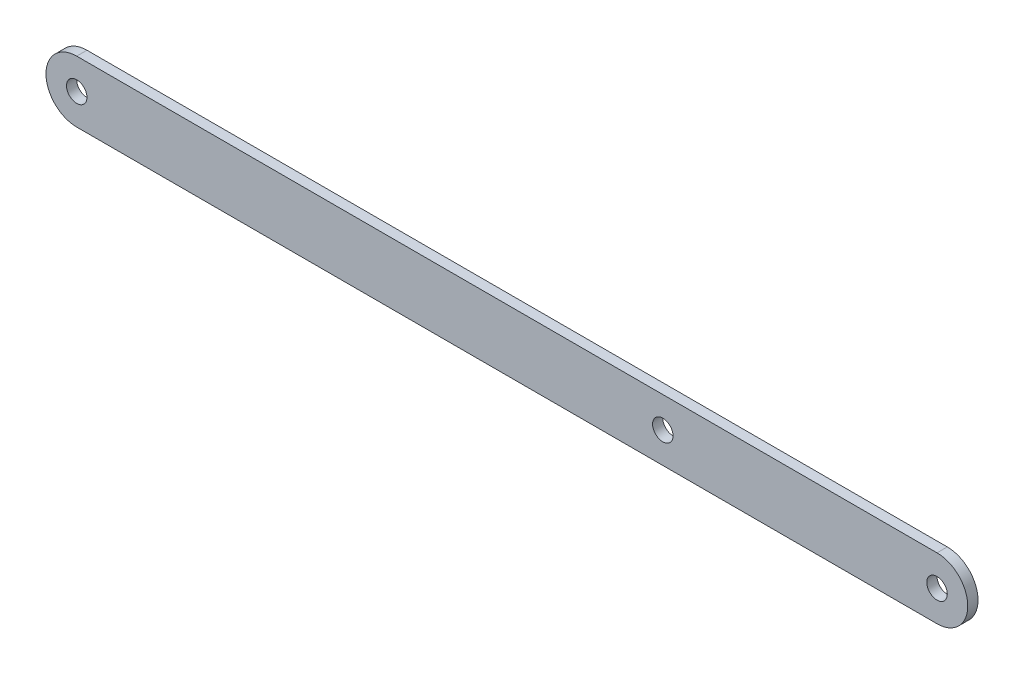
SolidWorks part; units mm, degrees
ref_plane "Front Plane" through (0, 0, 0) normal (0, 0, 1) x (1, 0, 0)
ref_plane "Top Plane" through (0, 0, 0) normal (0, 1, 0) x (1, 0, 0)
ref_plane "Right Plane" through (0, 0, 0) normal (1, 0, 0) x (0, 0, -1)
sketch "Sketch2" plane through (0, 0, 0) normal (0, 0, 1) x (1, 0, 0)
  line L0 (0, 38.1) -> (1066.8, 38.1)
  line L1 (1066.8, -38.1) -> (0, -38.1)
  arc A0 (0, 38.1) -> (0, -38.1) centre (0, 0) ccw
  circle A1 centre (0, 0) radius 12.7
  arc A38 (1066.8, -38.1) -> (1066.8, 38.1) centre (1066.8, 0) ccw
  circle A39 centre (1066.8, 0) radius 12.7
  dimension "D1" = 76.2
  dimension "D2" = 25.4
  dimension "D3" = 1066.8
extrude "Boss-Extrude1" add sketch "Sketch2" along normal blind 12.7
sketch "Sketch3" plane through (0, 0, 12.7) normal (0, 0, 1) x (1, 0, 0)
  circle A0 centre (726.7721, 0) radius 12.7
  dimension "D1" = 25.4
extrude "Cut-Extrude1" cut sketch "Sketch3" against normal through all
